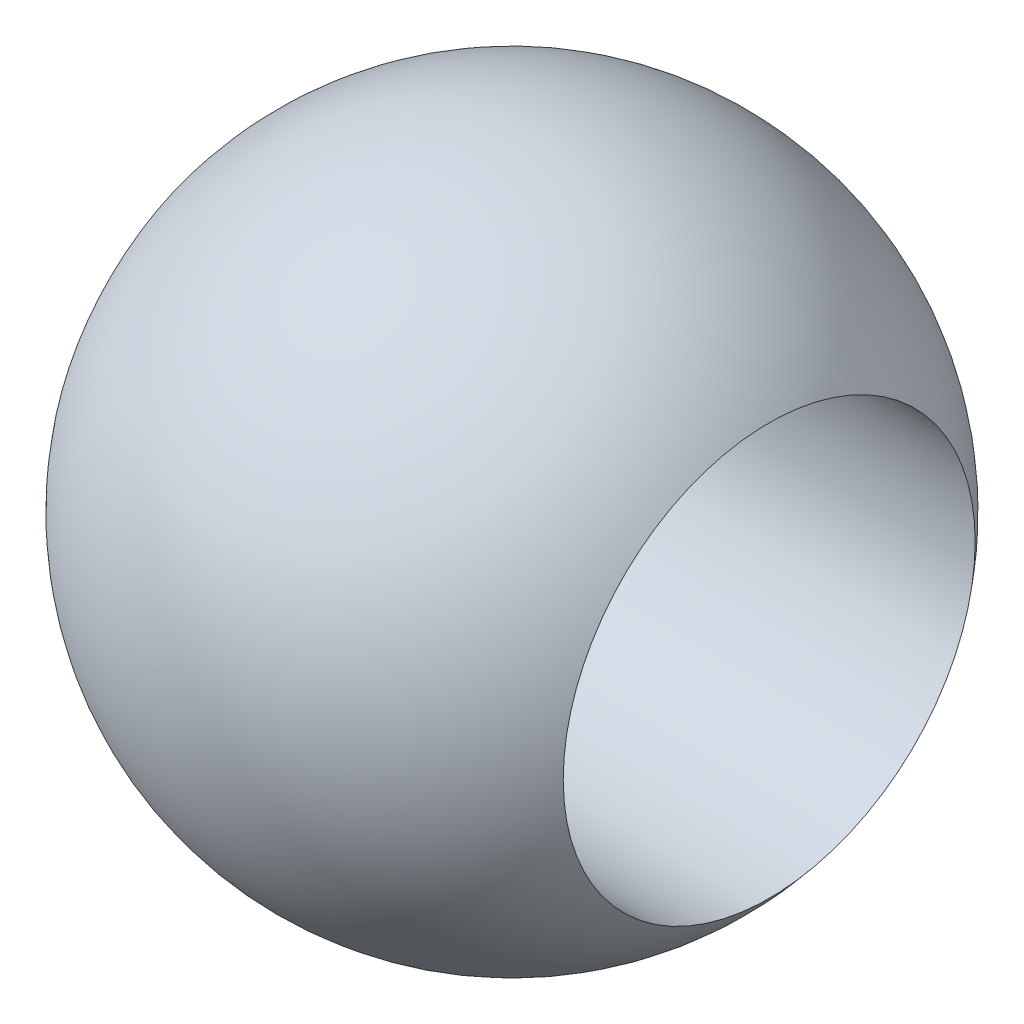
SolidWorks part; units mm, degrees
ref_plane "Front Plane" through (0, 0, 0) normal (0, 0, 1) x (1, 0, 0)
ref_plane "Top Plane" through (0, 0, 0) normal (0, 1, 0) x (1, 0, 0)
ref_plane "Right Plane" through (0, 0, 0) normal (1, 0, 0) x (0, 0, -1)
sketch "Sketch1" plane through (0, 0, 0) normal (0, 0, 1) x (1, 0, 0)
  line L0 (11.3859, 0) -> (-8.128, 0) construction
  line L5 (-6.3449, 5.08) -> (6.3449, 5.08)
  arc A0 (6.3449, 5.08) -> (-6.3449, 5.08) centre (0, 0) ccw
  dimension "D1" = 8.128
  dimension "D2" = 6.3449
revolve "Revolve1" add sketch "Sketch1" angle 360 about L0
